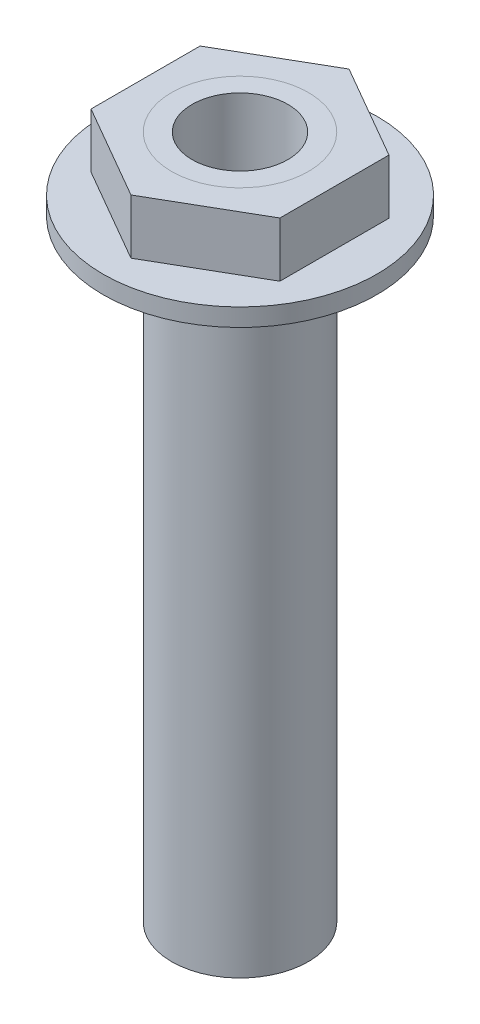
SolidWorks part; units mm, degrees
other "washer"
other "M10 nut"
ref_plane "Front Plane" through (0, 0, 0) normal (0, 0, 1) x (1, 0, 0)
ref_plane "Top Plane" through (0, 0, 0) normal (0, 1, 0) x (1, 0, 0)
ref_plane "Right Plane" through (0, 0, 0) normal (1, 0, 0) x (0, 0, -1)
sketch "Sketch1" plane through (0, 0, 0) normal (0, 1, 0) x (1, 0, 0)
  circle A0 centre (0, 0) radius 3.5
  circle A1 centre (0, 0) radius 5
  dimension "D1" = 10
  dimension "D2" = 7
extrude "Boss-Extrude1" add sketch "Sketch1" along normal blind 50
sketch "Sketch2" plane through (0, 50, 0) normal (0, 1, 0) x (1, 0, 0)
  line L1 (0, 7.9674) -> (-6.9, 3.9837)
  line L2 (-6.9, 3.9837) -> (-6.9, -3.9837)
  line L3 (-6.9, -3.9837) -> (0, -7.9674)
  line L4 (0, -7.9674) -> (6.9, -3.9837)
  line L5 (6.9, -3.9837) -> (6.9, 3.9837)
  line L6 (6.9, 3.9837) -> (0, 7.9674)
  circle A0 centre (0, 0) radius 5 construction
  circle A1 centre (0, 0) radius 5
  circle A2 centre (0, 0) radius 6.9 construction
  dimension "D1" = 13.8
extrude "Boss-Extrude2" add sketch "Sketch2" against normal blind 4 separate body
sketch "Sketch3" plane through (0, 46, 0) normal (0, -1, 0) x (1, 0, 0)
  circle A0 centre (0, 0) radius 10
  circle A1 centre (0, 0) radius 5
  circle A2 centre (0, 0) radius 5
  dimension "D2" = 20
  dimension "D1" = 0
extrude "Boss-Extrude3" add sketch "Sketch3" along normal blind 1.3 separate body
